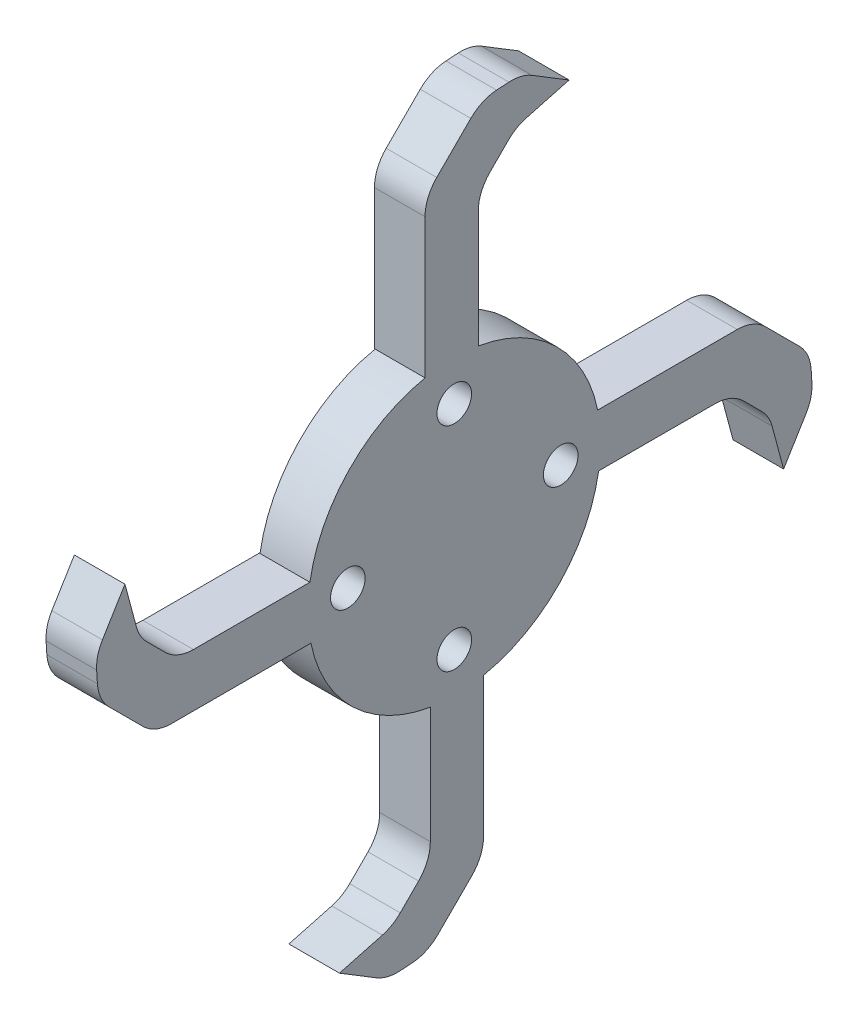
SolidWorks part; units mm, degrees
ref_plane "Front Plane" through (0, 0, 0) normal (0, 0, 1) x (1, 0, 0)
ref_plane "Top Plane" through (0, 0, 0) normal (0, 1, 0) x (1, 0, 0)
ref_plane "Right Plane" through (0, 0, 0) normal (1, 0, 0) x (0, 0, -1)
sketch "Sketch1" plane through (0, 0, 0) normal (1, 0, 0) x (0, 0, -1)
  circle A0 centre (0, 0) radius 13.97
  circle A1 centre (-10.16, 0) radius 1.651
  circle A2 centre (0, 10.16) radius 1.651
  circle A3 centre (10.16, 0) radius 1.651
  circle A4 centre (0, -10.16) radius 1.651
  point P14 (0, 0)
  dimension "D1" = 27.94
  dimension "D2" = 3.302
  dimension "D4" = 4
  dimension "D3" = 10.16
extrude "Boss-Extrude1" add sketch "Sketch1" along normal blind 4.7625
sketch "Sketch2" plane through (4.7625, 0, 0) normal (1, 0, 0) x (0, 0, -1)
  line L0 (13.6882, 2.7918) -> (28.5855, 2.7918)
  line L1 (13.7813, -2.2882) -> (26.4813, -2.2882)
  line L2 (28.5855, 2.7918) -> (33.9737, -2.5964)
  line L3 (26.4813, -2.2882) -> (30.0734, -5.8803)
  line L4 (30.0734, -5.8803) -> (31.4346, -10.9603)
  line L5 (33.9737, -2.5964) -> (34.2119, -6.4064)
  line L6 (34.2119, -6.4064) -> (31.4346, -10.9603)
  circle A1 centre (0, 0) radius 13.97 construction
  arc A3 (13.7813, -2.2882) -> (13.6882, 2.7918) centre (0, 0) ccw
  point P0 (0, 0)
  dimension "D2" = 14.8973
  dimension "D3" = 5.08
  dimension "D4" = 12.7
  dimension "D5" = 45
  dimension "D6" = 7.62
  dimension "D7" = 5.08
  dimension "D8" = 5.08
  dimension "D9" = 5.08
  dimension "D10" = 30
  dimension "D11" = 5.334
  dimension "D12" = 3.81
extrude "leg1" add sketch "Sketch2" against normal blind 4.826
fillet "Fillet2" radius 3.81 5 edges at (2.3495, -5.8803, -30.0734) (2.3495, -2.2882, -26.4813) (2.3495, -6.4064, -34.2119) (2.3495, -2.5964, -33.9737) (2.3495, 2.7918, -28.5855)
pattern_circular "CirPattern1" count 4 over 360 about axis through (0, 0, 0) along (1, 0, 0) of "Fillet2", "leg1"
